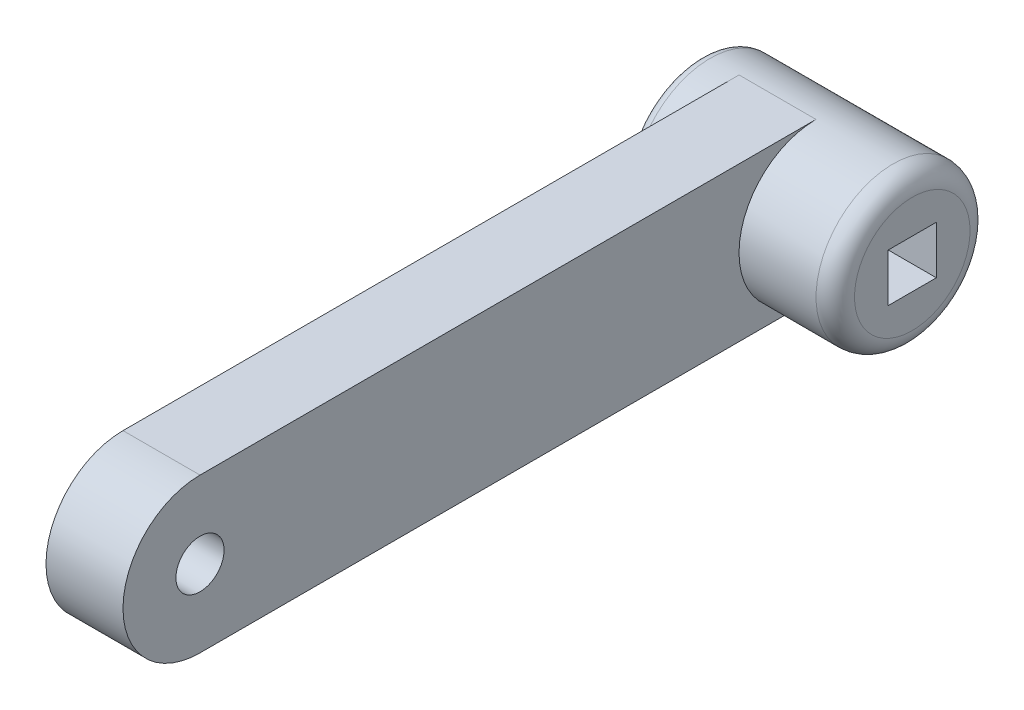
SolidWorks part; units mm, degrees
ref_plane "Front Plane" through (0, 0, 0) normal (0, 0, 1) x (1, 0, 0)
ref_plane "Top Plane" through (0, 0, 0) normal (0, 1, 0) x (1, 0, 0)
ref_plane "Right Plane" through (0, 0, 0) normal (1, 0, 0) x (0, 0, -1)
sketch "Sketch1" plane through (0, 0, 0) normal (1, 0, 0) x (0, 0, -1)
  circle A0 centre (0, 0) radius 10.16
  dimension "D1" = 20.32
extrude "Boss-Extrude1" add sketch "Sketch1" along normal mid plane 20.32
fillet "Fillet1" radius 1.27 1 edges at (-10.16, 0, -10.16)
sketch "Sketch2" plane through (0, 0, 0) normal (1, 0, 0) x (0, 0, -1)
  line L0 (-81.28, 0) -> (0, 0) construction
  line L1 (-81.28, 10.16) -> (0, 10.16)
  line L2 (-81.28, -10.16) -> (0, -10.16)
  arc A0 (-81.28, 10.16) -> (-81.28, -10.16) centre (-81.28, 0) ccw
  arc A1 (0, -10.16) -> (0, 10.16) centre (0, 0) ccw
  circle A2 centre (0, 0) radius 10.16 construction
  point P3 (-40.64, 0)
  dimension "D1" = 81.28
extrude "Boss-Extrude2" add sketch "Sketch2" along normal mid plane 10.16
sketch "Sketch3" plane through (10.16, 0, 0) normal (1, 0, 0) x (0, 0, -1)
  circle A0 centre (0, 0) radius 10.16
  arc A1 (0, 10.16) -> (0, -10.16) centre (0, 0) ccw construction
extrude "Boss-Extrude3" add sketch "Sketch3" along normal blind 7.62
fillet "Fillet2" radius 2.54 1 edges at (17.78, 0, -10.16)
sketch "Sketch4" plane through (17.78, 0, 0) normal (1, 0, 0) x (0, 0, -1)
  line L1 (-3.175, 3.175) -> (3.175, 3.175)
  line L2 (-3.175, 3.175) -> (-3.175, -3.175)
  line L3 (-3.175, -3.175) -> (3.175, -3.175)
  line L4 (3.175, 3.175) -> (3.175, -3.175)
  line L5 (-3.175, 3.175) -> (3.175, -3.175) construction
  line L6 (-3.175, -3.175) -> (3.175, 3.175) construction
  point P0 (0, 0)
  dimension "D1" = 6.35
extrude "Cut-Extrude1" cut sketch "Sketch4" against normal blind 25.4
sketch "Sketch5" plane through (5.08, 0, 0) normal (1, 0, 0) x (0, 0, -1)
  circle A0 centre (-81.28, 0) radius 3.175
  arc A1 (-81.28, 10.16) -> (-81.28, -10.16) centre (-81.28, 0) ccw construction
  dimension "D1" = 6.35
extrude "Cut-Extrude2" cut sketch "Sketch5" against normal through all
